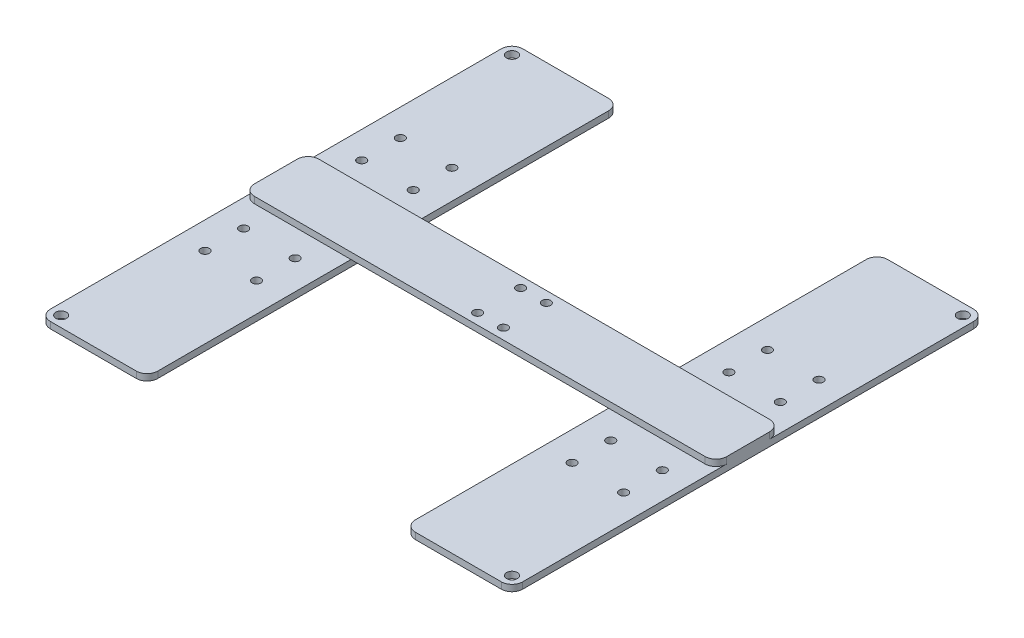
SolidWorks part; units mm, degrees
ref_plane "Front Plane" through (0, 0, 0) normal (0, 0, 1) x (1, 0, 0)
ref_plane "Top Plane" through (0, 0, 0) normal (0, 1, 0) x (1, 0, 0)
ref_plane "Right Plane" through (0, 0, 0) normal (1, 0, 0) x (0, 0, -1)
sketch "Sketch1" plane through (0, 0, 0) normal (0, 1, 0) x (1, 0, 0)
  line L1 (-110, -15) -> (110, -15)
  line L2 (-110, -15) -> (-110, 15)
  line L3 (-110, 15) -> (110, 15)
  line L4 (110, -15) -> (110, 15)
  line L5 (-110, -15) -> (110, 15) construction
  line L6 (-110, 15) -> (110, -15) construction
  point P0 (0, 0)
  dimension "D1" = 220
  dimension "D2" = 30
extrude "Boss-Extrude1" add sketch "Sketch1" along normal blind 3
sketch "Sketch2" plane through (0, 0, 0) normal (0, -1, 0) x (1, 0, 0)
  line L0 (-110, 0) -> (-85, 0) construction
  line L1 (-110, -15) -> (-110, 15) construction
  line L2 (0, 0) -> (0, -110) construction
  line L3 (-110, -110) -> (-60, -110)
  line L4 (-110, -110) -> (-110, 110)
  line L5 (-110, 110) -> (-60, 110)
  line L6 (-60, -110) -> (-60, 110)
  line L7 (-110, -110) -> (-60, 110) construction
  line L8 (-110, 110) -> (-60, -110) construction
  line L9 (110, 110) -> (60, 110)
  line L10 (60, -110) -> (60, 110)
  line L11 (110, -110) -> (60, -110)
  line L12 (110, -110) -> (110, 110)
  dimension "D1" = 25
  dimension "D2" = 50
  dimension "D3" = 220
  dimension "D4" = 110
extrude "Boss-Extrude2" add sketch "Sketch2" along normal blind 3
sketch "Sketch3" plane through (0, 0, 0) normal (0, 1, 0) x (1, 0, 0)
  line L0 (-110, 110) -> (-60, 110) construction
  line L1 (-110, 15) -> (-110, 110) construction
  line L2 (0, 15) -> (0, -15) construction
  line L3 (110, 15) -> (-110, 15) construction
  line L4 (-110, -15) -> (110, -15) construction
  line L5 (-110, 0) -> (110, 0) construction
  line L6 (-110, 15) -> (-110, -15) construction
  line L7 (110, -15) -> (110, 15) construction
  circle A0 centre (-105, 105) radius 2.5
  circle A1 centre (105, 105) radius 2.5
  circle A2 centre (105, -105) radius 2.5
  circle A3 centre (-105, -105) radius 2.5
  dimension "D1" = 5
  dimension "D2" = 5
  dimension "D3" = 5
extrude "Cut-Extrude1" cut sketch "Sketch3" against normal blind 3
fillet "Fillet1" radius 5 12 edges at (110, 1.5, 15) (110, 1.5, -15) (60, -1.5, 110) (110, -1.5, 110) (110, -1.5, -110) (60, -1.5, -110) (-60, -1.5, -110) (-110, -1.5, -110) (-110, 1.5, -15) (-110, 1.5, 15) (-60, -1.5, 110) (-110, -1.5, 110)
sketch "Sketch4" plane through (0, 0, 0) normal (0, 1, 0) x (1, 0, 0)
  line L0 (-60, 15) -> (-105, 15) construction
  line L1 (-110, 10) -> (-110, 105) construction
  line L2 (-110, 0) -> (110, 0) construction
  line L3 (-110, 10) -> (-110, -10) construction
  line L4 (110, -10) -> (110, 10) construction
  line L5 (0, 15) -> (0, -15) construction
  line L6 (105, 15) -> (-105, 15) construction
  line L7 (-105, -15) -> (105, -15) construction
  circle A0 centre (-97.5, 27.5) radius 2
  circle A1 centre (-73.5, 27.5) radius 2
  circle A2 centre (-73.5, 45.5) radius 2
  circle A3 centre (-97.5, 45.5) radius 2
  circle A4 centre (97.5, 45.5) radius 2
  circle A5 centre (73.5, 45.5) radius 2
  circle A6 centre (73.5, 27.5) radius 2
  circle A7 centre (97.5, 27.5) radius 2
  circle A8 centre (97.5, -27.5) radius 2
  circle A9 centre (73.5, -27.5) radius 2
  circle A10 centre (73.5, -45.5) radius 2
  circle A11 centre (97.5, -45.5) radius 2
  circle A12 centre (-97.5, -45.5) radius 2
  circle A13 centre (-73.5, -45.5) radius 2
  circle A14 centre (-73.5, -27.5) radius 2
  circle A15 centre (-97.5, -27.5) radius 2
  dimension "D1" = 12.5
  dimension "D2" = 12.5
  dimension "D3" = 4
  dimension "D4" = 2
  dimension "D6" = 24
  dimension "D7" = 18
  dimension "D8" = 12.5
  dimension "D5" = 2
extrude "Cut-Extrude2" cut sketch "Sketch4" against normal up to next
sketch "Sketch5" plane through (0, 3, 0) normal (0, 1, 0) x (1, 0, 0)
  line L0 (105, 15) -> (-105, 15) construction
  line L1 (0, 15) -> (0, -15) construction
  line L2 (-105, -15) -> (105, -15) construction
  line L3 (-110, 0) -> (110, 0) construction
  line L4 (-110, 10) -> (-110, -10) construction
  line L5 (110, -10) -> (110, 10) construction
  circle A0 centre (-6, 10) radius 2
  circle A1 centre (6, 10) radius 2
  circle A2 centre (6, -10) radius 2
  circle A3 centre (-6, -10) radius 2
  dimension "D1" = 4
  dimension "D2" = 5
  dimension "D3" = 6
extrude "Cut-Extrude3" cut sketch "Sketch5" against normal up to next
